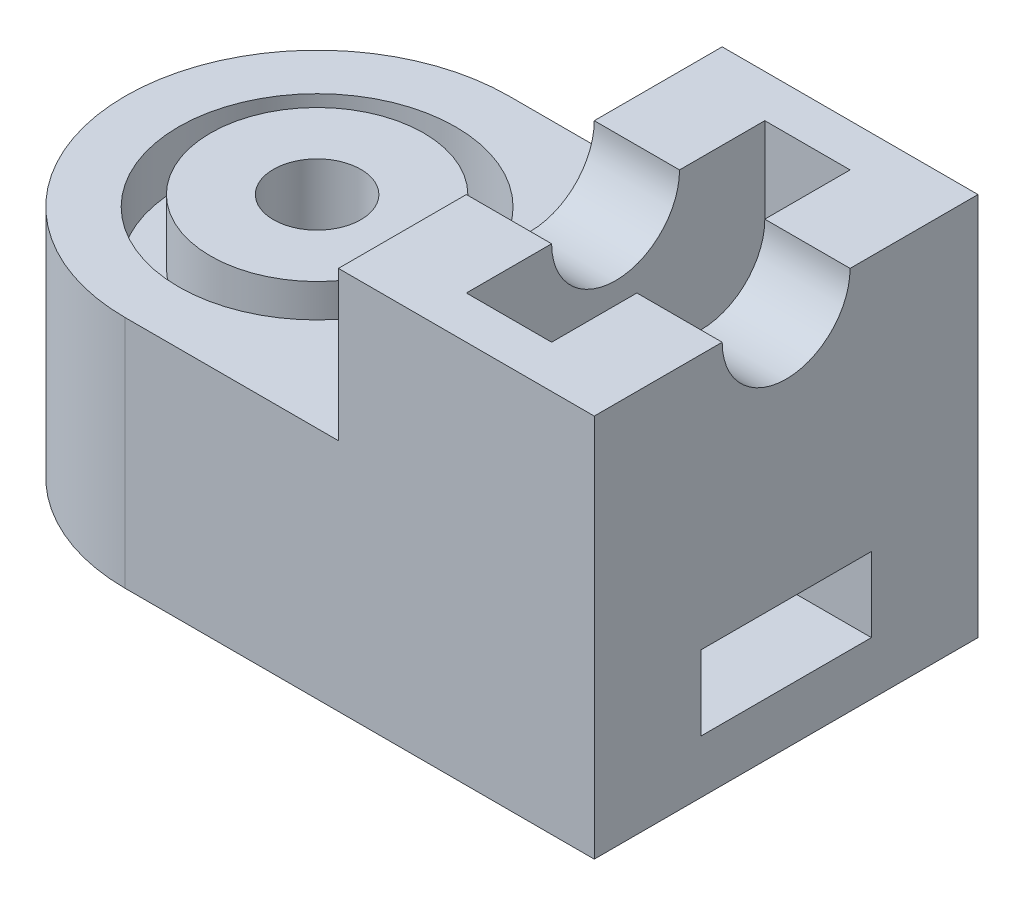
SolidWorks part; units mm, degrees
ref_plane "Front" through (0, 0, 0) normal (0, 0, 1) x (1, 0, 0)
ref_plane "Top" through (0, 0, 0) normal (0, 1, 0) x (1, 0, 0)
ref_plane "Right" through (0, 0, 0) normal (1, 0, 0) x (0, 0, -1)
sketch "Sketch2" plane through (0, 0, 0) normal (0, 1, 0) x (1, 0, 0)
  line L1 (-5.5, -4.5) -> (5.5, -4.5)
  line L2 (-5.5, -4.5) -> (-5.5, 4.5)
  line L3 (-5.5, 4.5) -> (5.5, 4.5)
  line L4 (5.5, -4.5) -> (5.5, 4.5)
  line L5 (-5.5, -4.5) -> (5.5, 4.5) construction
  line L6 (-5.5, 4.5) -> (5.5, -4.5) construction
  arc A0 (-5.5, 4.5) -> (-5.5, -4.5) centre (-5.5, 0) ccw
  point P0 (0, 0)
  dimension "D1" = 11
  dimension "D2" = 9
extrude "Boss-Extrude1" add sketch "Sketch2" along normal blind 9 contours L2 A0 | L1 L4 L3 L2
sketch "Sketch3" plane through (0, 9, 0) normal (0, 1, 0) x (1, 0, 0)
  line L0 (-5.5, 4.5) -> (5.5, 4.5) construction
  line L1 (-0.5, 4.5) -> (-16.3598, 4.5)
  line L2 (-0.5, 4.5) -> (-0.5, -5.4995)
  line L3 (-0.5, -5.4995) -> (-16.3598, -5.4995)
  line L4 (-16.3598, 4.5) -> (-16.3598, -5.4995)
  line L5 (5.5, -4.5) -> (5.5, 4.5) construction
  dimension "D1" = 6
extrude "Cut-Extrude1" cut sketch "Sketch3" against normal blind 3.5
sketch "Sketch4" plane through (-0.5, 0, 0) normal (-1, 0, 0) x (0, 0, 1)
  line L0 (4.5, 9) -> (-4.5, 9) construction
  line L1 (-4.5, 5.5) -> (-4.5, 9) construction
  line L2 (-1.5, 9) -> (1.5, 9)
  arc A0 (-1.5, 9) -> (1.5, 9) centre (0, 9) ccw
  dimension "D1" = 3
  dimension "D2" = 3
extrude "Cut-Extrude2" cut sketch "Sketch4" against normal blind 13.5
sketch "Sketch5" plane through (0, 9, 0) normal (0, 1, 0) x (1, 0, 0)
  line L0 (-0.5, 4.5) -> (5.5, 4.5) construction
  line L1 (3.5, 3.5) -> (1.5, 3.5)
  line L2 (3.5, 3.5) -> (3.5, -3.5)
  line L3 (3.5, -3.5) -> (1.5, -3.5)
  line L4 (1.5, 3.5) -> (1.5, -3.5)
  line L5 (-0.5, -4.5) -> (5.5, -4.5) construction
  line L6 (5.5, 1.5) -> (5.5, 4.5) construction
  line L7 (-0.5, -4.5) -> (-0.5, 4.5) construction
  dimension "D1" = 1
  dimension "D2" = 1
  dimension "D3" = 2
  dimension "D4" = 2
extrude "Cut-Extrude3" cut sketch "Sketch5" against normal blind 28.774
sketch "Sketch6" plane through (0, 5.5, 0) normal (0, 1, 0) x (1, 0, 0)
  circle A0 centre (-5.5, 0) radius 3.25
extrude "Cut-Extrude4" cut sketch "Sketch6" against normal blind 1.25
sketch "Sketch7" plane through (0, 4.25, 0) normal (0, 1, 0) x (1, 0, 0)
  circle A0 centre (-5.5, 0) radius 2.5
extrude "Boss-Extrude2" add sketch "Sketch7" along normal blind 1.5
sketch "Sketch8" plane through (5.5, 0, 0) normal (1, 0, 0) x (0, 0, -1)
  line L0 (-4.5, 0) -> (4.5, 0) construction
  line L1 (2, 1.25) -> (-2, 1.25)
  line L2 (2, 1.25) -> (2, 3)
  line L3 (2, 3) -> (-2, 3)
  line L4 (-2, 1.25) -> (-2, 3)
  line L5 (4.5, 5.5) -> (4.5, 0) construction
  line L6 (-4.5, 5.5) -> (-4.5, 0) construction
  line L7 (4.5, 5.5) -> (-4.5, 5.5) construction
  dimension "D1" = 1.25
  dimension "D2" = 2.5
  dimension "D3" = 2.5
  dimension "D4" = 2.5
extrude "Cut-Extrude5" cut sketch "Sketch8" against normal blind 21.5
ref_plane "Plane1" through (-10, 0, 0) normal (1, 0, 0) x (0, 0, -1)
sketch "Sketch9" plane through (-10, 0, 0) normal (1, 0, 0) x (0, 0, -1)
  line L0 (-4.5, 0) -> (4.5, 0) construction
  line L1 (-3, 0.75) -> (3, 0.75)
  line L2 (-3, 0.75) -> (-3, 3.5)
  line L3 (-3, 3.5) -> (3, 3.5)
  line L4 (3, 0.75) -> (3, 3.5)
  line L5 (4.5, 5.5) -> (4.5, 0) construction
  line L6 (-4.5, 5.5) -> (-4.5, 0) construction
  line L7 (4.5, 5.5) -> (-4.5, 5.5) construction
  dimension "D1" = 0.75
  dimension "D2" = 1.5
  dimension "D3" = 1.5
  dimension "D4" = 2
extrude "Cut-Extrude6" cut sketch "Sketch9" along normal blind 4.5
hole_wizard "M2.5 Tapped Hole2" positions "3DSketch1" profile "Sketch10" tap size "M2.5" standard "ISO"
sketch3d "3DSketch1"
  line L0 (-5.5, 5.75, 0) -> (-5.5, 4.25, 0) construction
  point P0 (-5.5, 5.75, 0)
sketch "Sketch10" plane through (-5.5, 5.75, 0) normal (1, 0, 0) x (0, 0, 1)
  line L0 (0, 0) -> (0, 3.6159)
  line L1 (0, 3.6159) -> (1.025, 3)
  line L2 (1.025, 3) -> (1.025, 0)
  line L5 (1.025, 0) -> (0, 0)
  line L10 (0, 3.6159) -> (-1.025, 3) construction
  line L11 (0, -6.35) -> (0, 107.95) construction
  dimension "Tap Drill Dia." = 2.05
  dimension "Tap Drill Depth" = 3
  dimension "Drill Angle" = 118
sketch "Sketch11" plane through (-5.5, 0, 0) normal (-1, 0, 0) x (0, 0, 1)
  line L0 (-1.025, 3.5) -> (1.025, 3.5)
  line L2 (-2, 1.25) -> (2, 1.25)
  line L3 (-2, 1.25) -> (-2, 3)
  line L4 (-2, 3) -> (2, 3)
  line L5 (2, 1.25) -> (2, 3)
  line L7 (1.025, 3.5) -> (1.025, 3)
  line L8 (1.025, 3.5) -> (1.025, 3)
  line L9 (-1.025, 3.5) -> (-3, 3.5)
  line L10 (-3, 3.5) -> (-3, 0.75)
  line L11 (-3, 0.75) -> (3, 0.75)
  line L12 (3, 0.75) -> (3, 3.5)
  line L13 (3, 3.5) -> (1.025, 3.5)
  line L16 (-1.025, 3.5) -> (-3, 3.5)
  line L17 (-3, 3.5) -> (-3, 0.75)
  line L18 (-3, 0.75) -> (3, 0.75)
  line L19 (3, 0.75) -> (3, 3.5)
  line L20 (3, 3.5) -> (1.025, 3.5)
  line L31 (1.025, 3) -> (2, 3)
  line L32 (1.025, 3) -> (2, 3)
  line L33 (2, 3) -> (2, 1.25)
  line L34 (2, 3) -> (2, 1.25)
  line L35 (2, 1.25) -> (-2, 1.25)
  line L36 (2, 1.25) -> (-2, 1.25)
  line L37 (-2, 1.25) -> (-2, 3)
  line L38 (-2, 1.25) -> (-2, 3)
  line L39 (-2, 3) -> (-1.025, 3)
  line L40 (-2, 3) -> (-1.025, 3)
  line L41 (-1.025, 3) -> (-1.025, 3.5)
  line L42 (-1.025, 3) -> (-1.025, 3.5)
  dimension "D1" = 0
extrude "Boss-Extrude3" add sketch "Sketch11" against normal blind 4
